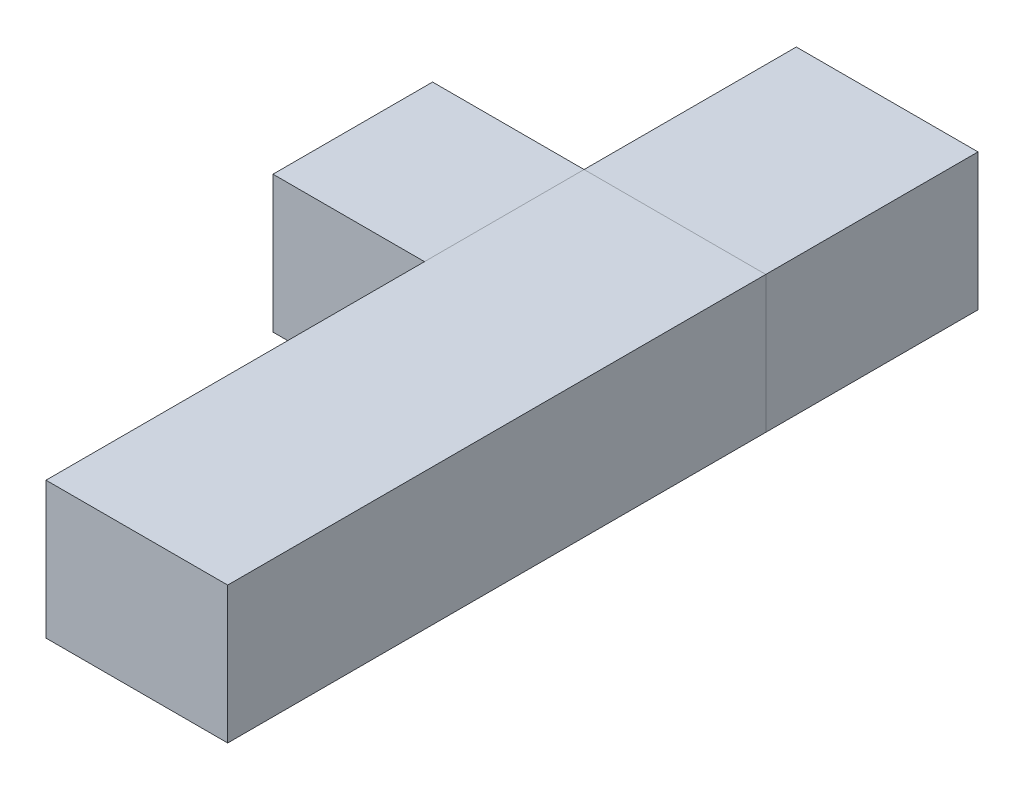
SolidWorks part; units mm, degrees
other "Best One"
material "A-Glass Fiber"
ref_plane "Front Plane" through (0, 0, 0) normal (0, 0, 1) x (1, 0, 0)
ref_plane "Top Plane" through (0, 0, 0) normal (0, 1, 0) x (1, 0, 0)
ref_plane "Right Plane" through (0, 0, 0) normal (1, 0, 0) x (0, 0, -1)
sketch "Sketch1" plane through (0, 0, 0) normal (1, 0, 0) x (0, 0, -1)
  line L0 (-12.7, 0) -> (12.7, 0) construction
  line L1 (-12.7, 9.652) -> (12.7, 9.652)
  line L2 (-12.7, 9.652) -> (-12.7, -9.398)
  line L3 (-12.7, -9.398) -> (12.7, -9.398)
  line L4 (12.7, 9.652) -> (12.7, -9.398)
  dimension "D1" = 19.05
  dimension "D2" = 25.4
  dimension "D3" = 9.652
extrude "Boss-Extrude1" add sketch "Sketch1" along normal mid plane 19.05
sketch "Sketch2" plane through (0, 0, 0) normal (1, 0, 0) x (0, 0, -1)
  line L0 (1.8599, -4.4901) -> (-3.048, -9.398)
  line L1 (-12.7, -9.398) -> (12.7, -9.398) construction
  line L2 (12.7, -9.398) -> (12.7, 9.652) construction
  line L3 (3.92, 5.8666) -> (2.352, 9.652)
  line L5 (2.352, 9.652) -> (-12.7, 9.652)
  line L6 (-12.7, 9.652) -> (-12.7, -9.398)
  line L7 (-12.7, -9.398) -> (-3.048, -9.398)
  line L8 (12.7, 9.652) -> (-12.7, 9.652) construction
  arc A0 (1.8599, -4.4901) -> (3.92, 5.8666) centre (6.35, 0) ccw
  dimension "D1" = 6.35
  dimension "D2" = 45
  dimension "D3" = 22.5
extrude "Cut-Extrude2" cut sketch "Sketch2" against normal through all both and the other way through all flip side to cut
sketch "Sketch3" plane through (0, 0, 0) normal (1, 0, 0) x (0, 0, -1)
  circle A0 centre (6.35, 0) radius 6.604
  arc A1 (1.8599, -4.4901) -> (3.92, 5.8666) centre (6.35, 0) ccw construction
  dimension "D1" = 13.208
extrude "Cut-Extrude3" cut sketch "Sketch3" against normal mid plane 12.954
sketch "Sketch5" plane through (0, 0, 0) normal (1, 0, 0) x (0, 0, -1)
  circle A0 centre (6.35, 0) radius 3.175
  arc A1 (1.8599, -4.4901) -> (3.92, 5.8666) centre (6.35, 0) ccw construction
  dimension "D1" = 6.35
extrude "Cut-Extrude5" cut sketch "Sketch5" against normal through all both and the other way through all
sketch "Sketch4" plane through (0, 0, 0) normal (0, 0, 1) x (1, 0, 0)
  line L0 (9.525, 9.652) -> (-9.525, 9.652) construction
  line L1 (-1.5875, 9.652) -> (1.5875, 9.652)
  line L2 (-1.5875, 9.652) -> (-1.5875, 4.7625)
  line L3 (-1.5875, 4.7625) -> (1.5875, 4.7625)
  line L4 (1.5875, 9.652) -> (1.5875, 4.7625)
  line L5 (0, -9.398) -> (0, 9.652) construction
  line L6 (9.525, -9.398) -> (-9.525, -9.398) construction
  dimension "D1" = 4.7625
  dimension "D2" = 3.175
extrude "Cut-Extrude4" cut sketch "Sketch4" against normal through all both and the other way through all
sketch "Sketch6" plane through (0, 0, 0) normal (1, 0, 0) x (0, 0, -1)
  line L0 (0, -6.35) -> (-3.048, -9.398)
  line L1 (-3.048, -9.398) -> (1.8599, -4.4901) construction
  line L2 (-3.048, -9.398) -> (-12.7, -9.398)
  line L3 (-12.7, -9.398) -> (-12.7, -6.35)
  line L4 (-12.7, 9.652) -> (-12.7, -9.398) construction
  line L5 (-12.7, -6.35) -> (0, -6.35)
  circle A0 centre (6.35, 0) radius 3.175 construction
  dimension "D1" = 6.35
extrude "Cut-Extrude6" cut sketch "Sketch6" against normal mid plane 3.175
sketch "Sketch7" plane through (0, 0, 0) normal (1, 0, 0) x (0, 0, -1)
  line L0 (1.7749, 4.7625) -> (-12.7, 4.7625) construction
  line L1 (-12.7, 9.652) -> (-3.81, 9.652)
  line L2 (-12.7, 9.652) -> (-12.7, 4.7625)
  line L3 (-12.7, 4.7625) -> (-3.81, 4.7625)
  line L4 (-3.81, 9.652) -> (-3.81, 4.7625)
  dimension "D1" = 3.81
extrude "Cut-Extrude7" cut sketch "Sketch7" against normal through all both and the other way through all
sketch "Sketch8" plane through (0, 0, 0) normal (1, 0, 0) x (0, 0, -1)
  line L0 (-3.81, 4.7625) -> (-3.81, 9.652) construction
  line L1 (-12.7, 4.7625) -> (-3.81, 4.7625)
  line L2 (-12.7, 4.7625) -> (-12.7, 1.9685)
  line L3 (-12.7, 1.9685) -> (-3.81, 1.9685)
  line L4 (-3.81, 4.7625) -> (-3.81, 1.9685)
  line L5 (-12.7, -9.398) -> (-3.81, -9.398)
  line L6 (-12.7, -9.398) -> (-12.7, -3.556)
  line L7 (-12.7, -3.556) -> (-3.81, -3.556)
  line L8 (-3.81, -9.398) -> (-3.81, -3.556)
  line L9 (-12.7, 4.7625) -> (-12.7, -9.398) construction
  line L11 (-12.7, -9.398) -> (-3.048, -9.398) construction
  dimension "D1" = 2.794
  dimension "D2" = 3.556
extrude "Cut-Extrude8" cut sketch "Sketch8" against normal through all both and the other way through all
sketch "Sketch9" plane through (0, 1.9685, 0) normal (0, 1, 0) x (1, 0, 0)
  line L0 (-9.525, -12.7) -> (9.525, -12.7) construction
  line L3 (-3.0668, -5.5282) -> (-9.525, -3.7978)
  line L4 (-9.525, -3.7978) -> (-9.525, -12.7)
  line L5 (-9.525, -12.7) -> (-9.525, -3.81) construction
  line L6 (-9.525, -12.7) -> (9.525, -12.7)
  line L7 (3.0668, -5.5282) -> (9.525, -3.7978)
  line L8 (9.525, -12.7) -> (9.525, -3.81) construction
  line L9 (9.525, -12.7) -> (9.525, -3.7978)
  arc A0 (3.0668, -5.5282) -> (-3.0668, -5.5282) centre (0, -6.35) cw
  dimension "D1" = 6.35
  dimension "D2" = 3.175
  dimension "D3" = 15
  dimension "D4" = 15
extrude "Cut-Extrude9" cut sketch "Sketch9" against normal through all both and the other way through all
sketch "Sketch11" plane through (0, 1.9685, 0) normal (0, 1, 0) x (1, 0, 0)
  circle A0 centre (0, -6.35) radius 0.5953
  arc A1 (-3.0668, -5.5282) -> (3.0668, -5.5282) centre (0, -6.35) ccw construction
  dimension "D1" = 1.1906
extrude "Cut-Extrude11" cut sketch "Sketch11" against normal through all
fillet "Fillet1" radius 3.175 2 edges at (9.525, 9.652, 0.7229) (-9.525, 9.652, 0.7229)
sketch "Sketch15" plane through (0, -3.556, 0) normal (0, -1, 0) x (1, 0, 0)
  circle A0 centre (0, 6.35) radius 4.064
  dimension "D1" = 8.128
extrude "Cut-Extrude12" cut sketch "Sketch15" along normal through all
sketch "Sketch22" plane through (0, 1.9685, 0) normal (0, 1, 0) x (1, 0, 0)
  circle A0 centre (0, -6.35) radius 4.064
  dimension "D1" = 8.128
extrude "Cut-Extrude15" cut sketch "Sketch22" along normal through all
sketch "Sketch16" plane through (9.525, 0, 0) normal (1, 0, 0) x (0, 0, -1)
  line L0 (-3.81, -4.7625) -> (1.5875, -4.7625) construction
  line L1 (-3.81, -9.398) -> (-3.81, -3.556) construction
  line L2 (-3.048, -9.398) -> (1.8599, -4.4901) construction
  line L3 (-3.7978, -9.398) -> (-3.7978, 6.477) construction
  line L5 (-0.6228, 0) -> (-3.7978, 0)
  line L6 (-0.6228, 0) -> (-0.6228, -6.9728)
  line L7 (-0.6228, -6.9728) -> (-3.7978, -6.9728)
  line L8 (-3.7978, 0) -> (-3.7978, -6.9728)
  dimension "D1" = 4.7625
  dimension "D2" = 3.175
extrude "Boss-Extrude4" add sketch "Sketch16" along normal blind 3.1267
sketch "Sketch18" plane through (-9.525, 0, 0) normal (-1, 0, 0) x (0, 0, 1)
  line L0 (3.7978, -9.398) -> (3.7978, 6.477) construction
  line L1 (0.6228, 0) -> (3.7978, 0)
  line L2 (0.6228, 0) -> (0.6228, -6.9728)
  line L3 (0.6228, -6.9728) -> (3.7978, -6.9728)
  line L4 (3.7978, 0) -> (3.7978, -6.9728)
  line L6 (3.048, -9.398) -> (-1.8599, -4.4901) construction
  dimension "D1" = 3.175
extrude "Boss-Extrude5" add sketch "Sketch18" along normal blind 3.1267
sketch "Sketch19" plane through (0, 0, 3.7978) normal (0, 0, 1) x (1, 0, 0)
  line L0 (11.0884, 0) -> (11.0884, -6.9728) construction
  line L1 (12.6517, 0) -> (9.525, 0) construction
  line L2 (12.6517, -6.9728) -> (9.525, -6.9728) construction
  circle A0 centre (11.0884, -4.7625) radius 0.7493
  dimension "D1" = 1.4986
  dimension "D2" = 4.7625
extrude "Cut-Extrude13" cut sketch "Sketch19" against normal through all
sketch "Sketch20" plane through (0, 0, 3.7978) normal (0, 0, 1) x (1, 0, 0)
  line L0 (-11.0884, -6.9728) -> (-11.0884, 0) construction
  line L1 (-12.6517, -6.9728) -> (-9.525, -6.9728) construction
  line L2 (-12.6517, 0) -> (-9.525, 0) construction
  circle A0 centre (-11.0884, -4.7625) radius 0.7493
  dimension "D1" = 1.4986
  dimension "D2" = 4.7625
extrude "Cut-Extrude14" cut sketch "Sketch20" against normal through all
sketch "Sketch26" plane through (0, 0, 0) normal (0, 0, 1) x (1, 0, 0)
  line L1 (12.6517, 9.652) -> (-33.7522, 9.652)
  line L2 (12.6517, 9.652) -> (12.6517, -9.398)
  line L3 (12.6517, -9.398) -> (-33.7522, -9.398)
  line L4 (-33.7522, 9.652) -> (-33.7522, -9.398)
ref_plane "Plane1" through (0, 0, 0) normal (0, -1, 0) x (-1, 0, 0)
extrude "Boss-Extrude8" add sketch "Sketch26" along normal through all and the other way through all separate body
ref_plane "Plane3" through (0, 0, 3.81) normal (0, 0, -1) x (-1, 0, 0)
sketch "Sketch23" plane through (0, 0, 0) normal (0, 1, 0) x (1, 0, 0)
  line L1 (-12.6517, 12.7) -> (12.6517, 12.7)
  line L2 (-12.6517, 12.7) -> (-12.6517, -62.2388)
  line L3 (-12.6517, -62.2388) -> (12.6517, -62.2388)
  line L4 (12.6517, 12.7) -> (12.6517, -62.2388)
extrude "Boss-Extrude6" add sketch "Sketch23" along normal through all and the other way through all separate body
sketch "Sketch24" plane through (0, 0, 0) normal (0, 1, 0) x (1, 0, 0)
  line L1 (-12.6517, -9.525) -> (12.6517, -9.525)
  line L2 (-12.6517, -9.525) -> (-12.6517, 42.2564)
  line L3 (-12.6517, 42.2564) -> (12.6517, 42.2564)
  line L4 (12.6517, -9.525) -> (12.6517, 42.2564)
extrude "Boss-Extrude7" add sketch "Sketch24" along normal through all and the other way through all separate body
ref_plane "Plane2" through (0, -6.9728, 0) normal (0, -1, 0) x (-1, 0, 0)
